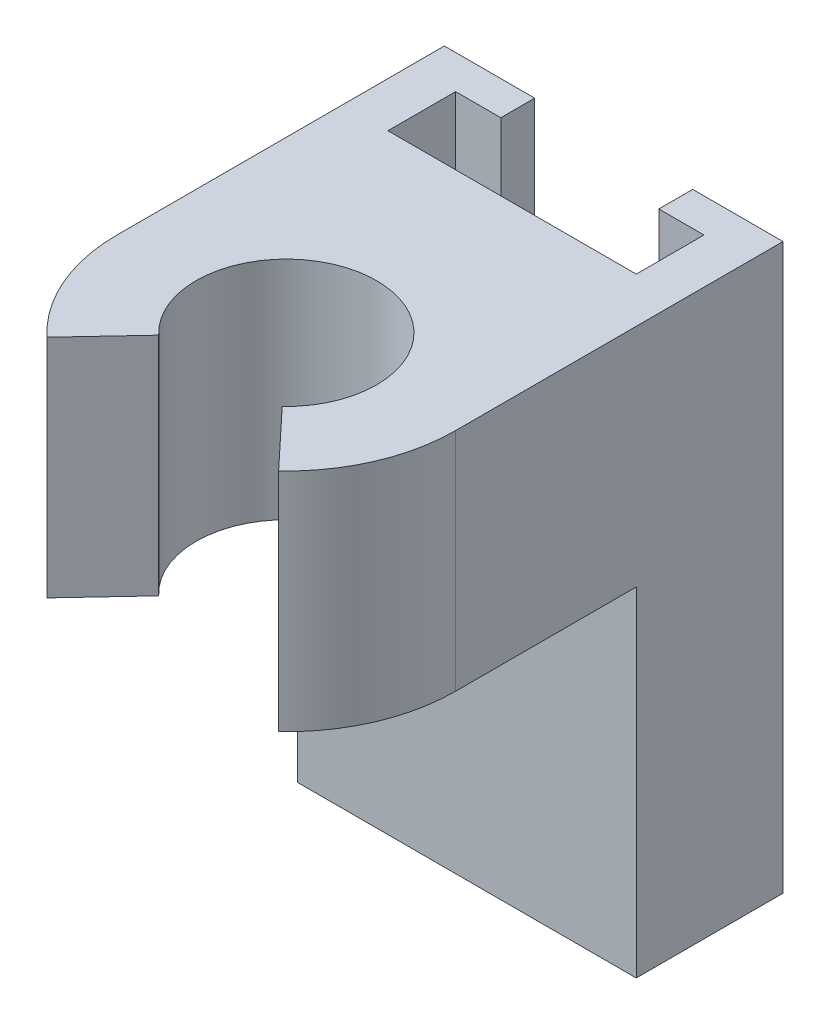
SolidWorks part; units mm, degrees
ref_plane "Front Plane" through (0, 0, 0) normal (0, 0, 1) x (1, 0, 0)
ref_plane "Top Plane" through (0, 0, 0) normal (0, 1, 0) x (1, 0, 0)
ref_plane "Right Plane" through (0, 0, 0) normal (1, 0, 0) x (0, 0, -1)
sketch "Sketch1" plane through (0, 0, 0) normal (0, 1, 0) x (1, 0, 0)
  line L0 (0, 0) -> (15, 0)
  line L1 (15, 0) -> (15, 6.5)
  line L2 (15, 6.5) -> (11, 6.5)
  line L3 (11, 6.5) -> (11, 5)
  line L4 (11, 5) -> (13, 5)
  line L5 (13, 5) -> (13, 2)
  line L6 (13, 2) -> (2, 2)
  line L7 (2, 2) -> (2, 5)
  line L8 (2, 5) -> (4, 5)
  line L9 (4, 5) -> (4, 6.5)
  line L10 (4, 6.5) -> (0, 6.5)
  line L11 (0, 6.5) -> (0, 0)
  dimension "D1" = 11
  dimension "D2" = 3
  dimension "D3" = 2
  dimension "D4" = 3
  dimension "D5" = 2
  dimension "D6" = 1.5
  dimension "D7" = 1.5
  dimension "D8" = 2
  dimension "D9" = 2
  dimension "D10" = 2
extrude "Boss-Extrude2" add sketch "Sketch1" along normal blind 25
sketch "Sketch2" plane through (0, 25, 0) normal (0, 1, 0) x (1, 0, 0)
  line L0 (7.5, 0) -> (7.5, -13.6617) construction
  line L1 (0, 0) -> (15, 0) construction
  line L3 (15, -8) -> (15, 0)
  line L4 (15, 0) -> (0, 0)
  line L5 (0, 0) -> (14.5313, -15.5) construction
  line L6 (15, 0) -> (0.8778, -15.0637) construction
  line L7 (10.2358, -10.9181) -> (12.6296, -13.4715)
  line L8 (4.7642, -10.9181) -> (2.3704, -13.4715)
  line L9 (0, 0) -> (0, -8)
  arc A0 (10.2358, -10.9181) -> (4.7642, -10.9181) centre (7.5, -8) ccw
  arc A1 (12.6296, -13.4715) -> (15, -8) centre (7.5, -8) ccw
  arc A2 (0, -8) -> (2.3704, -13.4715) centre (7.5, -8) ccw
  point P15 (10.2358, -10.9181)
extrude "Boss-Extrude3" add sketch "Sketch2" against normal blind 10
